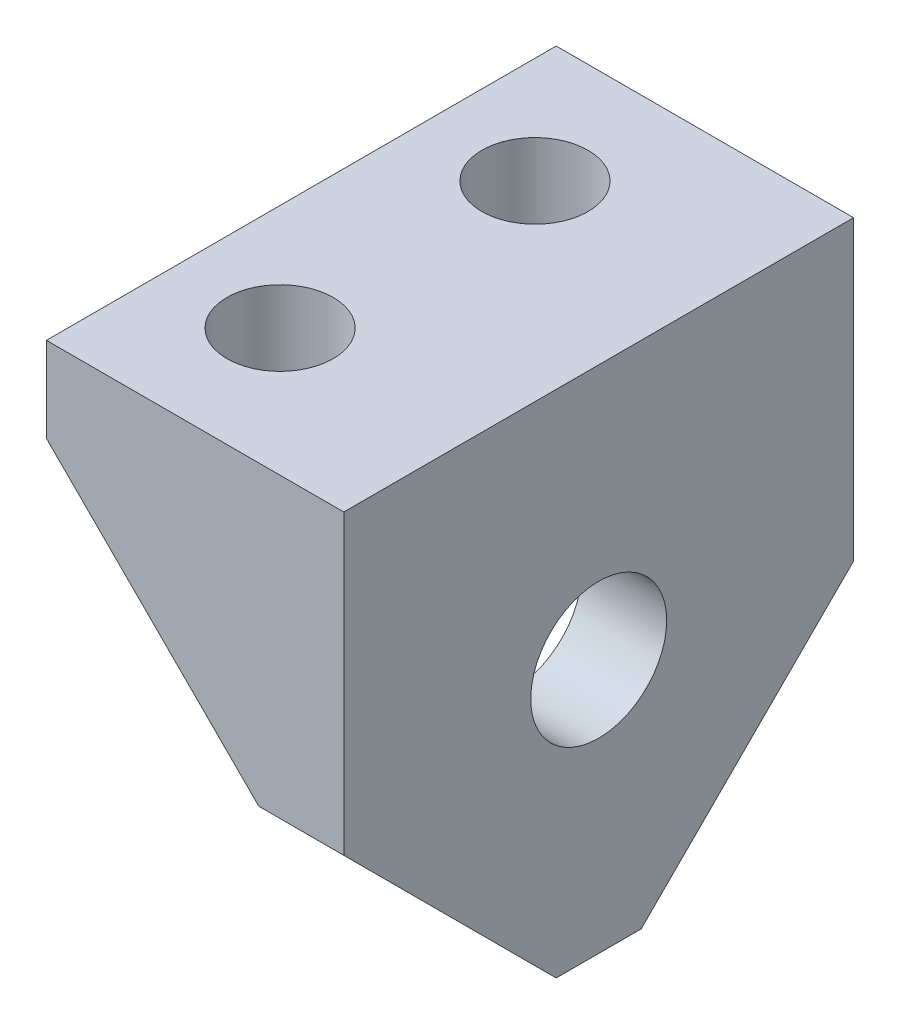
SolidWorks part; units mm, degrees
ref_plane "Front Plane" through (0, 0, 0) normal (0, 0, 1) x (1, 0, 0)
ref_plane "Top Plane" through (0, 0, 0) normal (0, 1, 0) x (1, 0, 0)
ref_plane "Right Plane" through (0, 0, 0) normal (1, 0, 0) x (0, 0, -1)
sketch "Sketch1" plane through (0, 0, 0) normal (1, 0, 0) x (0, 0, -1)
  line L1 (-6, 4.5) -> (6, 4.5)
  line L2 (-6, 4.5) -> (-6, -7.5)
  line L3 (-6, -7.5) -> (6, -7.5)
  line L4 (6, 4.5) -> (6, -7.5)
  dimension "D1" = 12
  dimension "D2" = 12
  dimension "D3" = 6
  dimension "D4" = 7.5
extrude "Boss-Extrude1" add sketch "Sketch1" along normal blind 2
sketch "Sketch3" plane through (0, 0, 0) normal (-1, 0, 0) x (0, 0, 1)
  line L0 (6, 4.5) -> (6, -7.5) construction
  line L1 (-6, 4.5) -> (6, 4.5)
  line L2 (-6, 4.5) -> (-6, 2.5)
  line L3 (-6, 2.5) -> (6, 2.5)
  line L4 (6, 4.5) -> (6, 2.5)
  dimension "D1" = 2
extrude "Boss-Extrude2" add sketch "Sketch3" along normal blind 5
sketch "Sketch4" plane through (2, 0, 0) normal (1, 0, 0) x (0, 0, -1)
  line L0 (-6, -7.5) -> (-6, -2.5) construction
  line L1 (-6, 4.5) -> (-6, -7.5) construction
  line L2 (-6, -2.5) -> (6, -2.5) construction
  line L3 (6, -7.5) -> (6, 4.5) construction
  line L4 (6, -2.5) -> (6, -7.5) construction
  line L5 (-6, -7.5) -> (-1, -7.5) construction
  line L6 (-6, -7.5) -> (6, -7.5) construction
  line L7 (0, 4.5) -> (0, -7.5) construction
  line L8 (6, 4.5) -> (-6, 4.5) construction
  line L9 (-6, -2.5) -> (-1, -7.5)
  line L10 (-1, -7.5) -> (-6, -7.5)
  line L11 (-6, -7.5) -> (-6, -2.5)
  line L12 (1, -7.5) -> (6, -7.5)
  line L13 (6, -2.5) -> (1, -7.5)
  line L14 (6, -7.5) -> (6, -2.5)
  dimension "D1" = 5
  dimension "D2" = 5
extrude "Cut-Extrude1" cut sketch "Sketch4" against normal blind 5
sketch "Sketch5" plane through (2, 0, 0) normal (1, 0, 0) x (0, 0, -1)
  line L0 (0, 4.5) -> (0, -7.5) construction
  line L1 (6, 4.5) -> (-6, 4.5) construction
  line L2 (-1, -7.5) -> (1, -7.5) construction
  line L3 (-6, 0) -> (6, 0) construction
  line L4 (-6, 4.5) -> (-6, -2.5) construction
  line L5 (6, -2.5) -> (6, 4.5) construction
  circle A1 centre (0, -1.5118) radius 1.6
  dimension "D1" = 3.2
extrude "Cut-Extrude2" cut sketch "Sketch5" against normal blind 5
sketch "Sketch7" plane through (0, 2.5, 0) normal (0, -1, 0) x (1, 0, 0)
  line L0 (-2.5, 6) -> (-2.5, -6) construction
  line L1 (-5, 6) -> (0, 6) construction
  line L2 (-5, -6) -> (0, -6) construction
  line L3 (-5, 0) -> (0, 0) construction
  line L4 (-5, -6) -> (-5, 6) construction
  circle A0 centre (-2.5, 3) radius 1.25
  circle A1 centre (-2.5, -3) radius 1.25
  dimension "D3" = 2.5
  dimension "D4" = 2.5
  dimension "D1" = 3
  dimension "D2" = 3
extrude "Cut-Extrude3" cut sketch "Sketch7" against normal blind 5
sketch "Sketch8" plane through (0, 0, 6) normal (0, 0, 1) x (1, 0, 0)
  line L0 (-5, 2.5) -> (0, 2.5) construction
  line L1 (-5, 2.5) -> (0, 2.5)
  line L2 (0, 2.5) -> (0, -2.5)
  line L3 (0, 2.5) -> (0, -2.5) construction
  line L4 (-5, 2.5) -> (0, -2.5)
  dimension "D1" = 5
extrude "Boss-Extrude4" add sketch "Sketch8" against normal blind 1.5
mirror "Mirror1" about plane through (0, 0, 0) normal (0, 0, 1) of "Boss-Extrude4"
